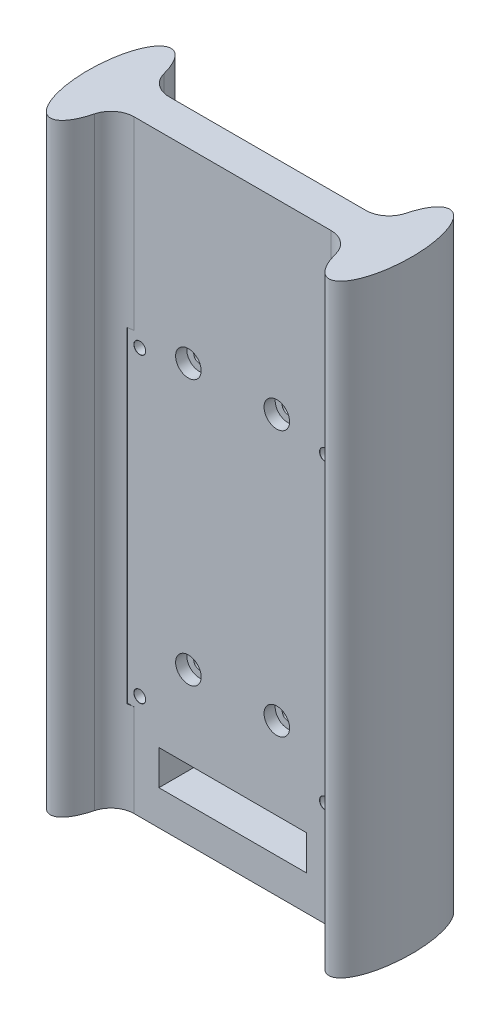
SolidWorks part; units mm, degrees
ref_plane "Front Plane" through (0, 0, 0) normal (0, 0, 1) x (1, 0, 0)
ref_plane "Top Plane" through (0, 0, 0) normal (0, 1, 0) x (1, 0, 0)
ref_plane "Right Plane" through (0, 0, 0) normal (1, 0, 0) x (0, 0, -1)
sketch "Sketch1" plane through (0, 0, 0) normal (0, 1, 0) x (1, 0, 0)
  line L0 (-30, 0) -> (-34.85, 0) construction
  line L1 (30, 3.75) -> (-30, 3.75)
  line L2 (30, 3.75) -> (30, -3.75)
  line L3 (30, -3.75) -> (-30, -3.75)
  line L4 (-30, 3.75) -> (-30, -3.75)
  line L5 (30, 3.75) -> (-30, -3.75) construction
  line L6 (30, -3.75) -> (-30, 3.75) construction
  line L7 (30, 0) -> (34.85, 0) construction
  ellipse E0 centre (-30, 0) end of major axis (-30, -13) minor radius 4.85
  ellipse E1 centre (30, 0) end of major axis (30, 13) minor radius 4.85
  point P0 (0, 0)
  dimension "D1" = 69.7
  dimension "D2" = 7.5
  dimension "D4" = 60
  dimension "D6" = 13
  dimension "D7" = 13
extrude "Boss-Extrude1" add sketch "Sketch1" along normal blind 130 contours E1 L1 E0 L3 | L3 E0 L1 L4 | L1 E0 L3 L4 | L1 E1 L3 L2 | L3 E1 L1 L2
fillet "Fillet1" radius 5 4 edges at (-25.3562, 65, -3.75) (25.3562, 65, -3.75) (25.3562, 65, 3.75) (-25.3562, 65, 3.75)
sketch "Sketch3" plane through (0, 0, -3.75) normal (0, 0, -1) x (-1, 0, 0)
  line L0 (0, 61.275) -> (0, 0) construction
  line L1 (15.875, 20) -> (-15.875, 20)
  line L2 (15.875, 20) -> (15.875, 102.55)
  line L3 (15.875, 102.55) -> (-15.875, 102.55)
  line L4 (-15.875, 20) -> (-15.875, 102.55)
  line L5 (15.875, 20) -> (-15.875, 102.55) construction
  line L6 (15.875, 102.55) -> (-15.875, 20) construction
  line L7 (21.1972, 0) -> (26.0334, 0) construction
  line L8 (-21.1972, 0) -> (21.1972, 0) construction
  line L9 (20.875, 102.55) -> (25.875, 102.55)
  line L10 (9.525, 32.7) -> (-9.525, 32.7)
  line L11 (9.525, 32.7) -> (9.525, 89.85)
  line L12 (9.525, 89.85) -> (-9.525, 89.85)
  line L13 (-9.525, 32.7) -> (-9.525, 89.85)
  line L14 (9.525, 32.7) -> (-9.525, 89.85) construction
  line L15 (9.525, 89.85) -> (-9.525, 32.7) construction
  line L16 (20.875, 102.55) -> (20.875, 20)
  line L17 (20.875, 20) -> (25.875, 20)
  line L18 (25.875, 102.55) -> (25.875, 20)
  line L20 (-15.875, 7.5) -> (15.875, 7.5)
  line L21 (-15.875, 7.5) -> (-15.875, 15)
  line L22 (-15.875, 15) -> (15.875, 15)
  line L23 (15.875, 7.5) -> (15.875, 15)
  point P0 (0, 61.275)
  dimension "D1" = 31.75
  dimension "D2" = 82.55
  dimension "D3" = 20
  dimension "D4" = 57.15
  dimension "D5" = 19.05
  dimension "D6" = 5
  dimension "D7" = 5
  dimension "D8" = 82.55
  dimension "D9" = 20
  dimension "D10" = 7.5
  dimension "D11" = 7.5
extrude "Cut-Extrude2" cut sketch "Sketch3" against normal through all both and the other way through all contours L21 L20 L23 L22
hole_wizard "Tap Drill for M3x0.5 Tap1" positions "3DSketch1" profile "Sketch4" hole size "M3x0.5" standard "ANSI Metric" end condition through all
sketch3d "3DSketch1"
  point P0 (9.525, 89.85, -3.75)
  point P3 (-9.525, 89.85, -3.75)
  point P6 (-9.525, 32.7, -3.75)
  point P9 (9.525, 32.7, -3.75)
sketch "Sketch4" plane through (9.525, 89.85, -3.75) normal (1, 0, 0) x (0, 1, 0)
  line L0 (0, 0) -> (0, 16.75)
  line L1 (0, 16.75) -> (1.25, 16.75)
  line L2 (1.25, 16.75) -> (1.25, 0)
  line L5 (1.25, 0) -> (0, 0)
  line L11 (0, -6.35) -> (0, 107.95) construction
  dimension "Thru Hole Dia." = 2.5
  dimension "Thru Hole Depth" = 16.75
sketch "Sketch5" plane through (0, 0, 3.75) normal (0, 0, 1) x (1, 0, 0)
  line L0 (-15.875, 15) -> (15.875, 15) construction
  line L1 (17.5, 25) -> (-17.5, 25)
  line L2 (17.5, 25) -> (17.5, 85)
  line L3 (17.5, 85) -> (-17.5, 85)
  line L4 (-17.5, 25) -> (-17.5, 85)
  line L5 (17.5, 25) -> (-17.5, 85) construction
  line L6 (17.5, 85) -> (-17.5, 25) construction
  line L7 (22.6, 19.9) -> (22.6, 90.1)
  line L8 (0, 15) -> (0, 55) construction
  line L9 (22.6, 90.1) -> (-22.6, 90.1)
  line L10 (-22.6, 19.9) -> (-22.6, 90.1)
  line L11 (22.6, 19.9) -> (-22.6, 19.9)
  line L12 (20, 22.5) -> (20, 87.5) construction
  line L13 (20, 87.5) -> (-20, 87.5) construction
  line L14 (-20, 22.5) -> (-20, 87.5) construction
  line L15 (20, 22.5) -> (-20, 22.5) construction
  point P0 (0, 55)
  dimension "D1" = 40
  dimension "D2" = 60
  dimension "D3" = 35
  dimension "D4" = 5.1
  dimension "D5" = 2.5
extrude "Cut-Extrude3" cut sketch "Sketch5" along normal blind 10
sketch "Sketch6" plane through (0, 0, 3.75) normal (0, 0, 1) x (1, 0, 0)
  circle A0 centre (9.525, 89.85) radius 2.75
  circle A1 centre (-9.525, 89.85) radius 2.75
  circle A2 centre (9.525, 32.7) radius 2.75
  circle A4 centre (-9.525, 32.7) radius 2.75
  dimension "D1" = 5.5
  dimension "D2" = 5.5
  dimension "D3" = 5.5
  dimension "D4" = 5.5
extrude "Cut-Extrude4" cut sketch "Sketch6" against normal blind 2.4
sketch "Sketch7" plane through (0, 0, 3.75) normal (0, 0, 1) x (1, 0, 0)
  point P0 (-20, 87.5)
  point P3 (20, 87.5)
  point P6 (20, 22.5)
  point P9 (-20, 22.5)
hole_wizard "Tap Drill for M3 Tap1" positions "Sketch7" profile "Sketch8" hole size "M3" standard "ISO" end condition through all
sketch "Sketch8" plane through (-20, 87.5, 3.75) normal (1, 0, 0) x (0, -1, 0)
  line L0 (0, 0) -> (0, 16.75)
  line L1 (0, 16.75) -> (1.25, 16.75)
  line L2 (1.25, 16.75) -> (1.25, 0.025)
  line L3 (1.25, 0.025) -> (1.275, 0)
  line L5 (1.275, 0) -> (0, 0)
  line L6 (-1.25, 0.025) -> (-1.275, 0) construction
  line L11 (0, -6.35) -> (0, 107.95) construction
  dimension "Thru Hole Dia." = 2.5
  dimension "Thru Hole Depth" = 16.75
  dimension "Near C'Sink Dia." = 2.55
  dimension "Near C'Sink Angle" = 90
